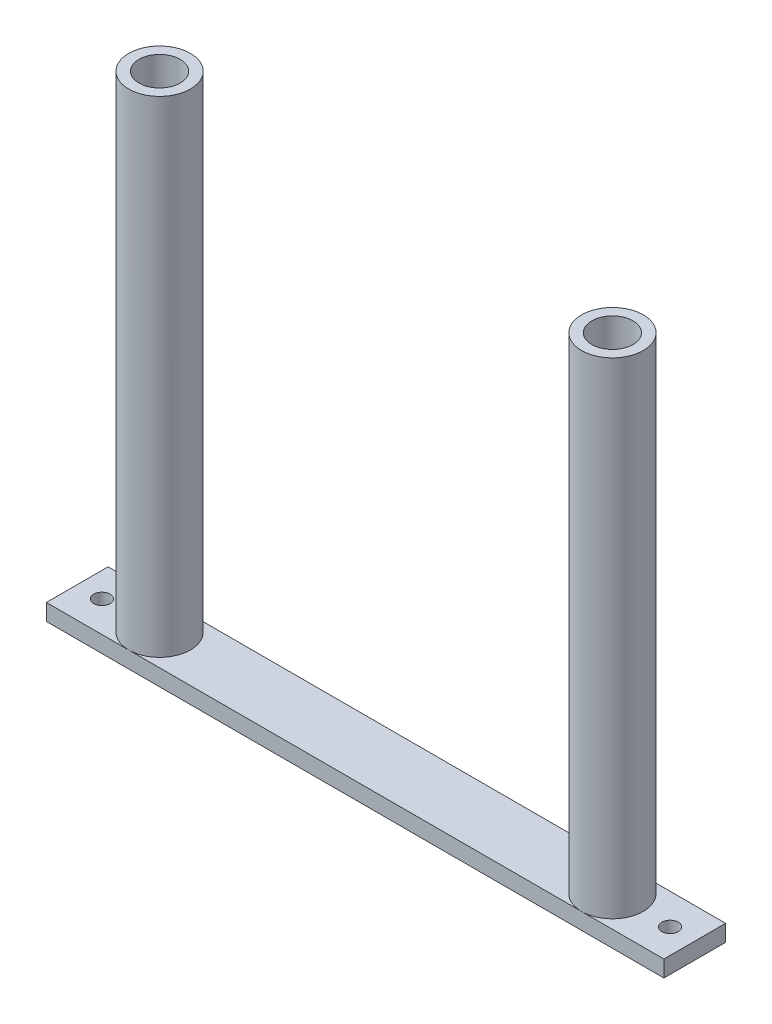
SolidWorks part; units mm, degrees
ref_plane "Front Plane" through (0, 0, 0) normal (0, 0, 1) x (1, 0, 0)
ref_plane "Top Plane" through (0, 0, 0) normal (0, 1, 0) x (1, 0, 0)
ref_plane "Right Plane" through (0, 0, 0) normal (1, 0, 0) x (0, 0, -1)
sketch "Sketch1" plane through (0, 0, 0) normal (0, 1, 0) x (1, 0, 0)
  line L5 (25.4, -9.525) -> (-25.4, -9.525)
  line L6 (25.4, -9.525) -> (25.4, 9.525)
  line L7 (25.4, 9.525) -> (-25.4, 9.525)
  line L8 (-25.4, -9.525) -> (-25.4, 9.525)
  line L9 (25.4, -9.525) -> (-25.4, 9.525) construction
  line L10 (25.4, 9.525) -> (-25.4, -9.525) construction
  point P0 (0, 0)
  dimension "D1" = 50.8
  dimension "D2" = 19.05
extrude "Boss-Extrude1" add sketch "Sketch1" along normal blind 5.08
sketch "Sketch2" plane through (0, 5.08, 0) normal (0, 1, 0) x (1, 0, 0)
  line L0 (25.4, 9.525) -> (-25.4, 9.525) construction
  circle A0 centre (0, 0) radius 9.525
extrude "Boss-Extrude2" add sketch "Sketch2" along normal blind 149.86
sketch "Sketch3" plane through (0, 154.94, 0) normal (0, 1, 0) x (1, 0, 0)
  circle A0 centre (0, 0) radius 6.35
  dimension "D1" = 12.7
extrude "Cut-Extrude1" cut sketch "Sketch3" against normal blind 81.28
sketch "Sketch4" plane through (0, 0, 0) normal (0, 0, 1) x (1, 0, 0)
  line L0 (9.525, 154.94) -> (-9.525, 154.94) construction
  line L1 (-9.525, 128.27) -> (9.525, 128.27) construction
  line L2 (9.525, 5.08) -> (9.525, 154.94) construction
  line L3 (-9.525, 154.94) -> (-9.525, 5.08) construction
  line L4 (-9.525, 123.19) -> (9.525, 123.19) construction
  line L5 (-9.525, 113.03) -> (9.525, 113.03) construction
  line L6 (-9.525, 92.71) -> (9.525, 92.71) construction
  circle A0 centre (0, 130.81) radius 1.27
  circle A1 centre (0, 125.73) radius 1.27
  circle A2 centre (0, 120.65) radius 1.27
  circle A3 centre (0, 115.57) radius 1.27
  circle A4 centre (0, 110.49) radius 1.27
  circle A5 centre (0, 105.41) radius 1.27
  circle A6 centre (0, 100.33) radius 1.27
  circle A7 centre (0, 95.25) radius 1.27
  circle A8 centre (0, 74.93) radius 1.27
  circle A9 centre (0, 80.01) radius 1.27
  circle A10 centre (0, 85.09) radius 1.27
  circle A11 centre (0, 90.17) radius 1.27
  dimension "D1" = 2.54
  dimension "D2" = 24.13
  dimension "D3" = 2.54
  dimension "D4" = 2.54
  dimension "D5" = 2.54
  dimension "D6" = 2.54
extrude "Cut-Extrude2" cut sketch "Sketch4" against normal through all
ref_plane "Plane1" through (69.85, 0, 0) normal (1, 0, 0) x (0, 0, -1)
sketch "Sketch6" plane through (0, 0, 9.525) normal (0, 0, 1) x (1, 0, 0)
  line L0 (25.4, 5.08) -> (69.85, 5.08)
  line L1 (69.85, -10.4775) -> (69.85, 10.4775) construction
  line L2 (69.85, 5.08) -> (69.85, 0)
  line L3 (69.85, 0) -> (25.4, 0)
  line L4 (25.4, 0) -> (25.4, 5.08)
extrude "Boss-Extrude3" add sketch "Sketch6" against normal through all
mirror "Mirror3" about plane through (69.85, 0, 0) normal (1, 0, 0) of bodies 105
sketch "Sketch7" plane through (0, 5.08, 0) normal (0, 1, 0) x (1, 0, 0)
  line L0 (-25.4, 9.525) -> (-25.4, -9.525) construction
  line L1 (165.1, 9.525) -> (165.1, -9.525) construction
  circle A0 centre (-17.78, 0) radius 2.54
  circle A1 centre (157.48, 0) radius 2.54
  point P4 (0, 0)
  point P6 (-14.5854, 0)
  point P7 (0, 0)
  dimension "D3" = 5.08
  dimension "D4" = 5.08
  dimension "D1" = 7.62
  dimension "D2" = 7.62
extrude "Cut-Extrude3" cut sketch "Sketch7" against normal through all
